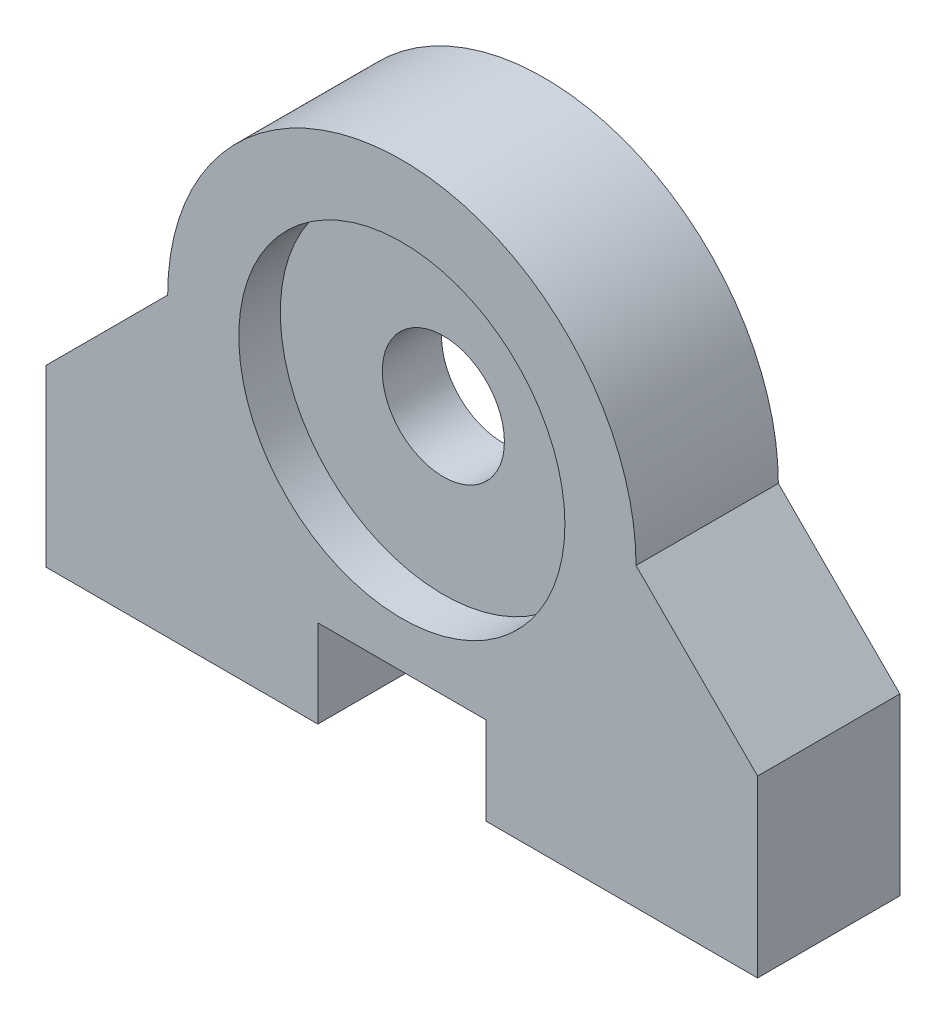
SolidWorks part; units mm, degrees
ref_plane "Front Plane" through (0, 0, 0) normal (0, 0, 1) x (1, 0, 0)
ref_plane "Top Plane" through (0, 0, 0) normal (0, 1, 0) x (1, 0, 0)
ref_plane "Right Plane" through (0, 0, 0) normal (1, 0, 0) x (0, 0, -1)
sketch "Sketch1" plane through (0, 0, 0) normal (0, 0, 1) x (1, 0, 0)
  line L0 (0, -26.1041) -> (0, 52.7781) construction
  line L1 (4.5, 4.699) -> (-4.5, 4.699)
  line L2 (-4.5, 4.699) -> (-4.5, 0)
  line L3 (-4.5, 0) -> (-19.05, 0)
  line L4 (19.05, 0) -> (19.05, 9.3663)
  line L5 (19.05, 9.3663) -> (12.5412, 15.875)
  line L6 (4.5, 4.699) -> (4.5, 0)
  line L7 (-19.05, 0) -> (-19.05, 9.3663)
  line L8 (4.5, 0) -> (19.05, 0)
  line L9 (-19.05, 9.3663) -> (-12.5412, 15.875)
  circle A0 centre (0, 15.875) radius 8.7312
  arc A1 (-12.5412, 15.875) -> (12.5412, 15.875) centre (0, 15.875) cw
  point P11 (0, 4.699)
  point P12 (0, 28.448)
  point P15 (0, 7.1438)
  dimension "D6" = 17.4625
  dimension "D3" = 3.81
  dimension "D1" = 9
  dimension "D2" = 4.699
  dimension "D4" = 45
  dimension "D5" = 15.875
  dimension "D7" = 38.1
extrude "Boss-Extrude1" add sketch "Sketch1" along normal blind 7.62
ref_plane "Plane1" through (0, 0, 3.81) normal (0, 0, 1) x (1, 0, 0)
sketch "Sketch3" plane through (0, 0, 3.81) normal (0, 0, 1) x (1, 0, 0)
  circle A0 centre (0, 15.875) radius 3.2703
  circle A1 centre (0, 15.875) radius 8.7376
  dimension "D1" = 6.5405
  dimension "D2" = 17.4752
extrude "Boss-Extrude2" add sketch "Sketch3" along normal blind 1.5875 and the other way blind 1.5875
sketch "Sketch4" plane through (0, 0, 0) normal (0, -1, 0) x (-1, 0, 0)
  line L0 (19.05, -3.81) -> (-19.9911, -3.81) construction
  line L1 (19.05, -7.62) -> (19.05, 0) construction
  line L2 (-15.6289, -3.81) -> (15.6289, -3.81) construction
  line L3 (0, 9.7586) -> (0, -18.8259) construction
  circle A0 centre (-11.43, -3.81) radius 1.9837
  circle A1 centre (11.43, -3.81) radius 1.9837
  dimension "D1" = 3.9675
  dimension "D2" = 11.43
extrude "Cut-Extrude1" cut sketch "Sketch4" against normal blind 10.16
equation "\"0.095inin\"=0.085"
